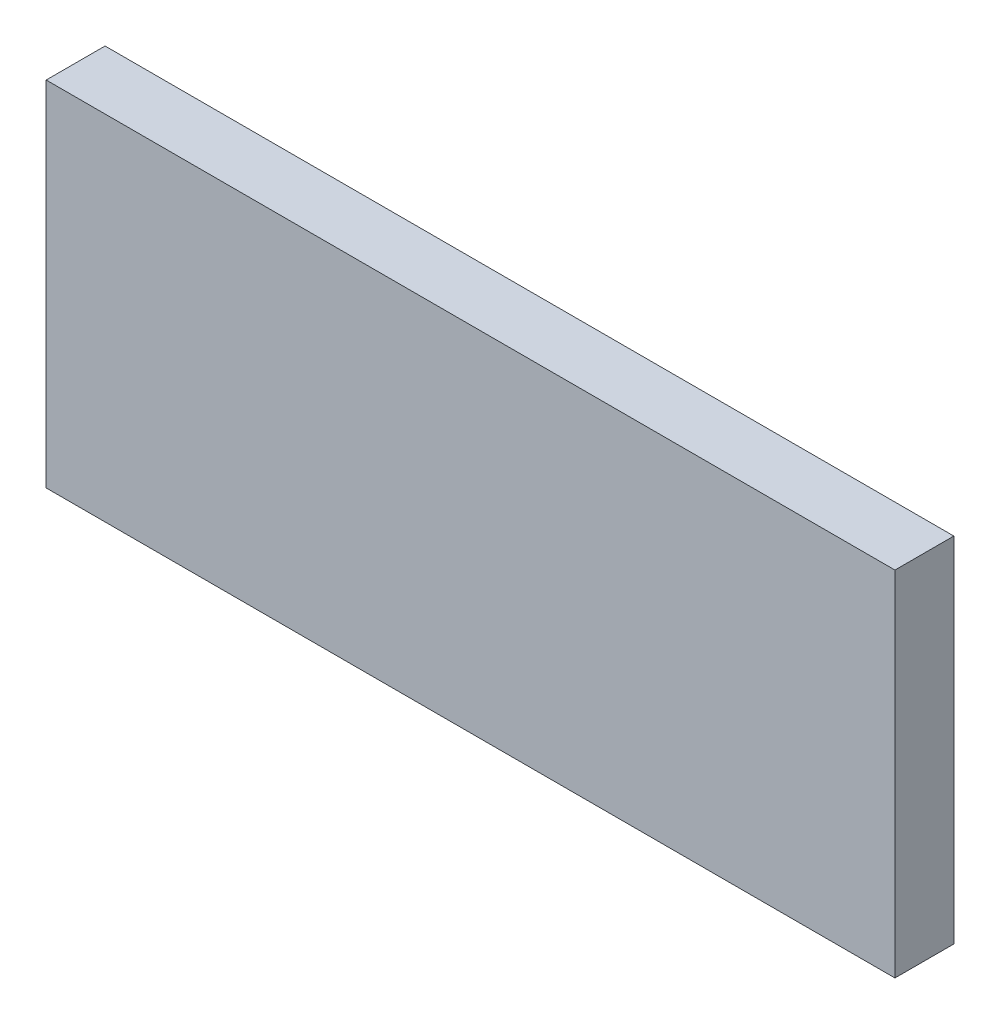
SolidWorks part; units mm, degrees
ref_plane "前基準面" through (0, 0, 0) normal (0, 0, 1) x (1, 0, 0)
ref_plane "上基準面" through (0, 0, 0) normal (0, 1, 0) x (1, 0, 0)
ref_plane "右基準面" through (0, 0, 0) normal (1, 0, 0) x (0, 0, -1)
sketch "草圖1" plane through (0, 0, 0) normal (0, 1, 0) x (1, 0, 0)
  line L1 (-36.035, -2.5) -> (36.035, -2.5)
  line L2 (-36.035, -2.5) -> (-36.035, 2.5)
  line L3 (-36.035, 2.5) -> (36.035, 2.5)
  line L4 (36.035, -2.5) -> (36.035, 2.5)
  line L5 (-36.035, -2.5) -> (36.035, 2.5) construction
  line L6 (-36.035, 2.5) -> (36.035, -2.5) construction
  point P0 (0, 0)
  dimension "D1" = 72.07
  dimension "D2" = 5
extrude "填料-伸長1" add sketch "草圖1" along normal blind 30
sketch "草圖2" plane through (0, 0, -2.5) normal (0, 0, -1) x (-1, 0, 0)
  line L0 (36.035, 19) -> (36.035, 11)
  line L1 (36.035, 30) -> (36.035, 0) construction
  line L2 (36.035, 11) -> (31.035, 11)
  line L3 (31.035, 11) -> (31.035, 9.75)
  line L4 (31.035, 9.75) -> (-1.465, 9.75)
  line L5 (-1.465, 9.75) -> (-1.465, 20.25)
  line L6 (-1.465, 20.25) -> (31.035, 20.25)
  line L7 (31.035, 20.25) -> (31.035, 19)
  line L8 (31.035, 19) -> (36.035, 19)
  line L9 (-36.035, 15) -> (-19.6481, 15) construction
  line L10 (-36.035, 0) -> (36.035, 0) construction
  line L11 (-36.035, 30) -> (36.035, 30) construction
  dimension "D1" = 5
  dimension "D2" = 10.5
  dimension "D3" = 8
  dimension "D4" = 32.5
extrude "除料-伸長1" cut sketch "草圖2" against normal blind 4
sketch "草圖3" plane through (0, 30, 0) normal (0, 1, 0) x (1, 0, 0)
  line L0 (31.835, 2.5) -> (31.835, -2.5) construction
  line L1 (36.035, 2.5) -> (-36.035, 2.5) construction
  line L2 (-36.035, -2.5) -> (36.035, -2.5) construction
  line L3 (36.035, -2.5) -> (36.035, 2.5) construction
  line L4 (33.365, 2.5) -> (31.835, -0.15)
  line L5 (31.835, -0.15) -> (27.2451, 2.5)
  line L6 (27.2451, 2.5) -> (33.365, 2.5)
  point P8 (36.035, 0)
  dimension "D1" = 4.2
  dimension "D2" = 30
  dimension "D3" = 2.35
extrude "除料-伸長2" cut sketch "草圖3" against normal mid plane 20.5 from offset 15
